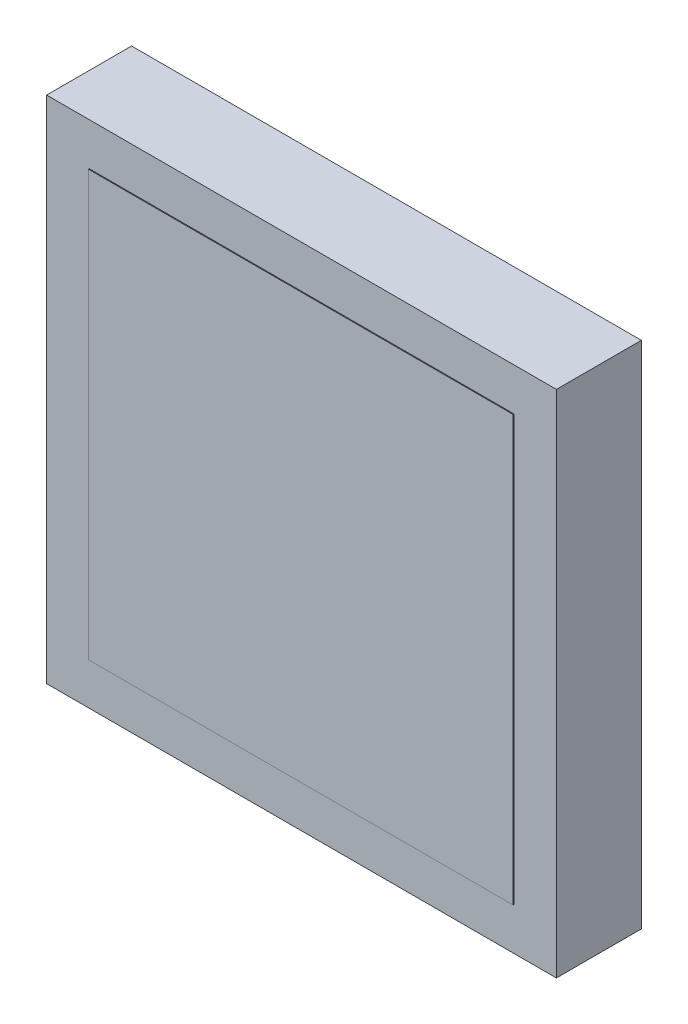
SolidWorks part; units mm, degrees
ref_plane "Front Plane" through (0, 0, 0) normal (0, 0, 1) x (1, 0, 0)
ref_plane "Top Plane" through (0, 0, 0) normal (0, 1, 0) x (1, 0, 0)
ref_plane "Right Plane" through (0, 0, 0) normal (1, 0, 0) x (0, 0, -1)
sketch "Sketch1" plane through (0, 0, 0) normal (0, 0, 1) x (1, 0, 0)
  line L1 (-30, -30) -> (30, -30)
  line L2 (-30, -30) -> (-30, 30)
  line L3 (-30, 30) -> (30, 30)
  line L4 (30, -30) -> (30, 30)
  line L5 (-30, -30) -> (30, 30) construction
  line L6 (-30, 30) -> (30, -30) construction
  point P0 (0, 0)
  dimension "D1" = 60
extrude "Boss-Extrude1" add sketch "Sketch1" along normal blind 10
sketch "Sketch2" plane through (0, 0, 10) normal (0, 0, 1) x (1, 0, 0)
  line L0 (-30, -30) -> (30, -30) construction
  line L1 (-25, -25) -> (25, -25)
  line L2 (-25, -25) -> (-25, 25)
  line L3 (-25, 25) -> (25, 25)
  line L4 (25, -25) -> (25, 25)
  line L5 (-25, -25) -> (25, 25) construction
  line L6 (-25, 25) -> (25, -25) construction
  line L7 (-30, 30) -> (-30, -30) construction
  point P0 (0, 0)
  dimension "D1" = 5
  dimension "D2" = 5
extrude "Boss-Extrude2" add sketch "Sketch2" along normal blind 0.1
